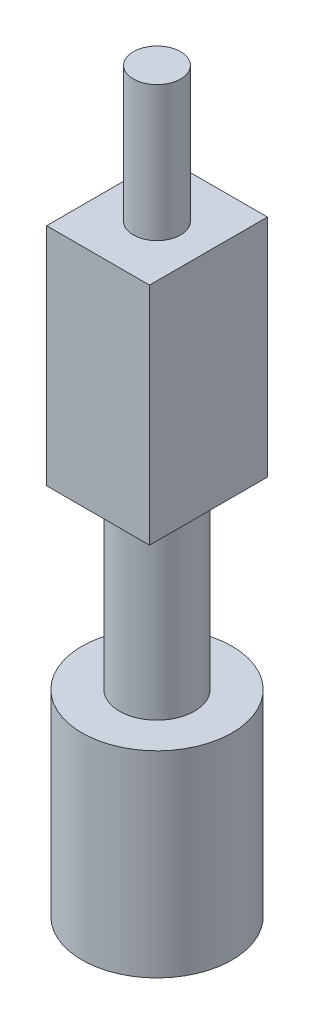
SolidWorks part; units mm, degrees
ref_plane "Front Plane" through (0, 0, 0) normal (0, 0, 1) x (1, 0, 0)
ref_plane "Top Plane" through (0, 0, 0) normal (0, 1, 0) x (1, 0, 0)
ref_plane "Right Plane" through (0, 0, 0) normal (1, 0, 0) x (0, 0, -1)
sketch "Sketch1" plane through (0, 0, 0) normal (0, 1, 0) x (1, 0, 0)
  line L1 (-6.85, -7.85) -> (6.85, -7.85)
  line L2 (-6.85, -7.85) -> (-6.85, 7.85)
  line L3 (-6.85, 7.85) -> (6.85, 7.85)
  line L4 (6.85, -7.85) -> (6.85, 7.85)
  line L5 (-6.85, -7.85) -> (6.85, 7.85) construction
  line L6 (-6.85, 7.85) -> (6.85, -7.85) construction
  point P0 (0, 0)
  dimension "D1" = 15.7
  dimension "D2" = 13.7
extrude "Boss-Extrude1" add sketch "Sketch1" along normal blind 30
sketch "Sketch2" plane through (0, 0, 0) normal (0, -1, 0) x (1, 0, 0)
  circle A0 centre (0, 0) radius 5
  dimension "D1" = 10
extrude "Boss-Extrude2" add sketch "Sketch2" along normal blind 24 contours A0
sketch "Sketch3" plane through (0, -24, 0) normal (0, -1, 0) x (1, 0, 0)
  circle A0 centre (0, 0) radius 10
  dimension "D1" = 20
extrude "Boss-Extrude3" add sketch "Sketch3" along normal blind 26.2
sketch "Sketch4" plane through (0, -50.2, 0) normal (0, -1, 0) x (1, 0, 0)
  circle A0 centre (0, 0) radius 5
  dimension "D1" = 10
extrude "Boss-Extrude4" add sketch "Sketch4" along normal blind 3
sketch "Sketch5" plane through (0, 30, 0) normal (0, 1, 0) x (1, 0, 0)
  circle A0 centre (0, 0) radius 3.15
  dimension "D1" = 6.3
extrude "Boss-Extrude5" add sketch "Sketch5" along normal blind 18
ref_plane "Plane1" through (-6.85, 30, -7.85) normal (-1, 0, 0) x (0, 0, 1)
sketch "Sketch8" plane through (0, 0, -7.85) normal (0, 0, -1) x (-1, 0, 0)
  line L0 (-6.85, 0) -> (6.85, 0) construction
  line L1 (-6.85, 30) -> (6.85, 30) construction
  circle A0 centre (0, 8) radius 1.5
  circle A1 centre (0, 22.8) radius 1.5
  point P4 (0, 0)
  point P7 (0, 0)
  point P10 (0, 30)
  point P11 (0, 20.9751)
  dimension "D1" = 3
  dimension "D2" = 14.8
  dimension "D3" = 8
extrude "Cut-Extrude1" cut sketch "Sketch8" against normal blind 2
